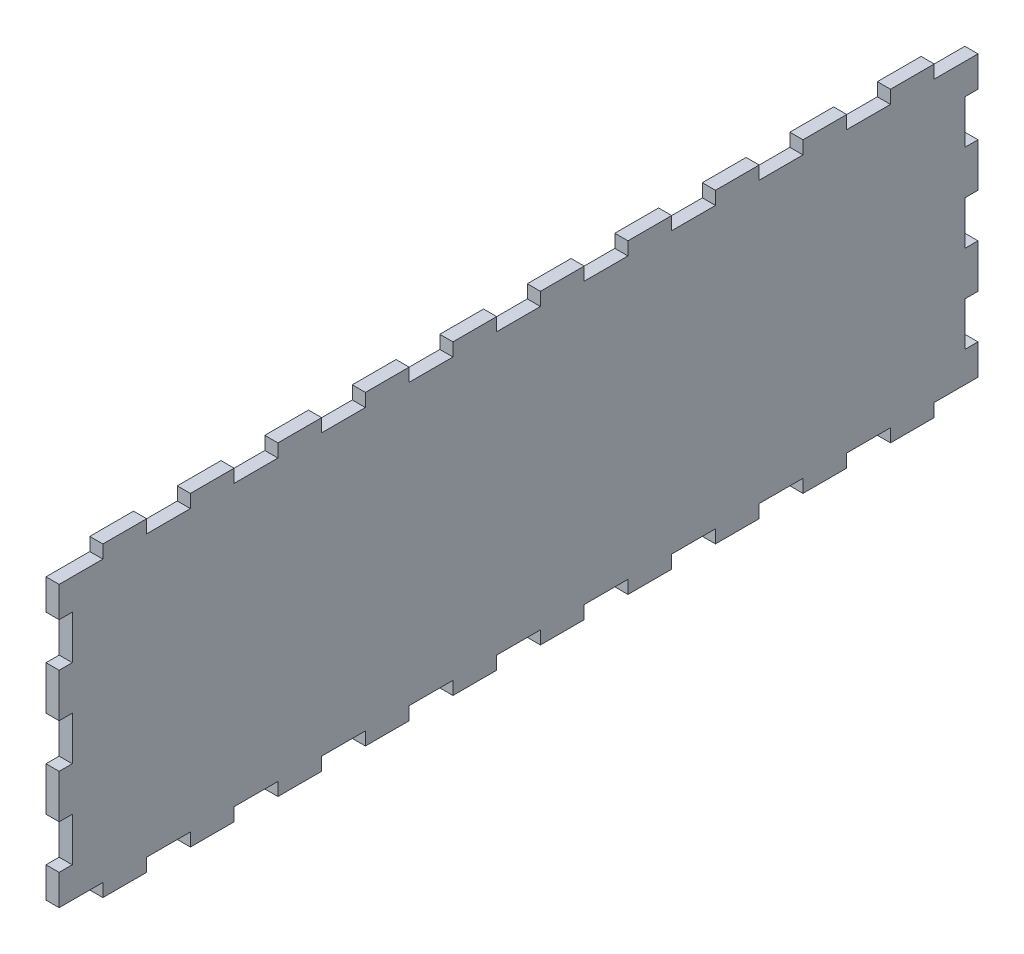
SolidWorks part; units mm, degrees
ref_plane "Front Plane" through (0, 0, 0) normal (0, 0, 1) x (1, 0, 0)
ref_plane "Top Plane" through (0, 0, 0) normal (0, 1, 0) x (1, 0, 0)
ref_plane "Right Plane" through (0, 0, 0) normal (1, 0, 0) x (0, 0, -1)
sketch "Sketch1" plane through (0, 0, 0) normal (1, 0, 0) x (0, 0, -1)
  line L1 (-105, -35) -> (105, -35)
  line L2 (-105, -35) -> (-105, 35)
  line L3 (-105, 35) -> (105, 35)
  line L4 (105, -35) -> (105, 35)
  line L5 (-105, -35) -> (105, 35) construction
  line L6 (-105, 35) -> (105, -35) construction
  point P0 (0, 0)
  dimension "D1" = 210
  dimension "D2" = 70
extrude "Boss-Extrude1" add sketch "Sketch1" along normal blind 3
sketch "Sketch2" plane through (3, 0, 0) normal (1, 0, 0) x (0, 0, -1)
  line L1 (-105, 35) -> (-95, 35)
  line L2 (-105, 35) -> (-105, 32)
  line L3 (-105, 32) -> (-95, 32)
  line L4 (-95, 35) -> (-95, 32)
  dimension "D1" = 10
  dimension "D2" = 3
extrude "Cut-Extrude1" cut sketch "Sketch2" against normal blind 3
pattern_linear "LPattern1" count 11 spacing 20 along (0, 0, -1) of "Cut-Extrude1"
mirror "Mirror1" about plane through (0, 0, 0) normal (0, 1, 0) of "LPattern1", "Cut-Extrude1"
sketch "Sketch3" plane through (3, 0, 0) normal (1, 0, 0) x (0, 0, -1)
  line L0 (-105, 32) -> (-105, -32) construction
  line L1 (-105, 25) -> (-102, 25)
  line L2 (-105, 25) -> (-105, 15)
  line L3 (-105, 15) -> (-102, 15)
  line L4 (-102, 25) -> (-102, 15)
  line L5 (-105, 32) -> (-95, 32) construction
  dimension "D1" = 10
  dimension "D2" = 3
  dimension "D3" = 7
extrude "Cut-Extrude2" cut sketch "Sketch3" against normal blind 3
pattern_linear "LPattern2" count 3 spacing 20 along (0, -1, 0) of "Cut-Extrude2"
mirror "Mirror2" about plane through (0, 0, 0) normal (0, 0, 1) of "LPattern2", "Cut-Extrude2"
